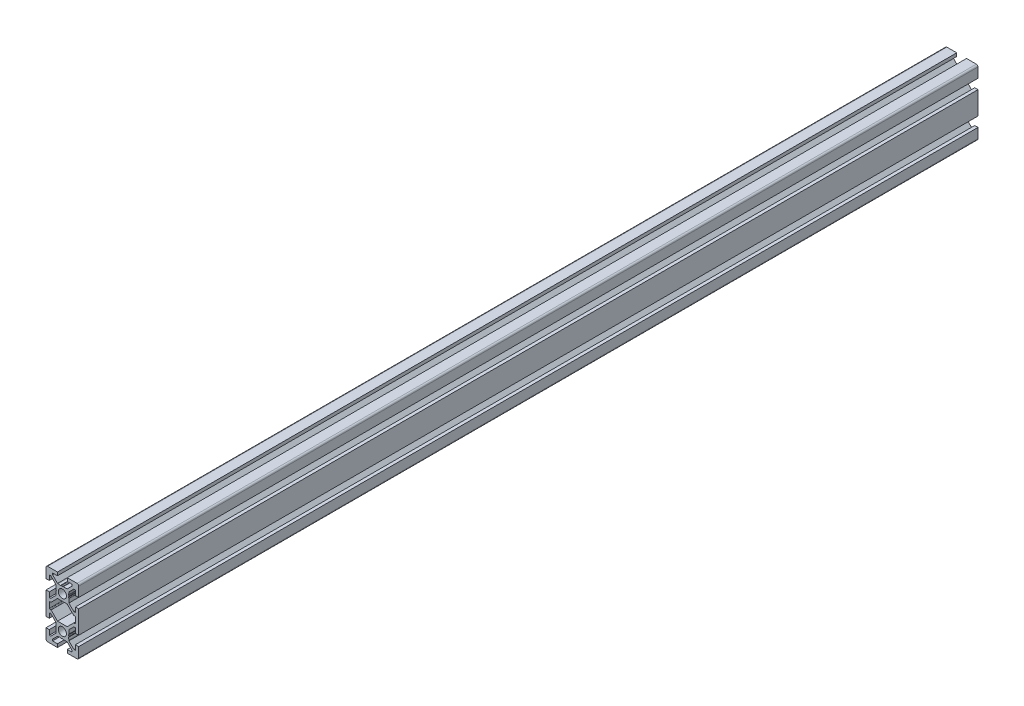
SolidWorks part; units mm, degrees
ref_plane "Front Plane" through (0, 0, 0) normal (0, 0, 1) x (1, 0, 0)
ref_plane "Top Plane" through (0, 0, 0) normal (0, 1, 0) x (1, 0, 0)
ref_plane "Right Plane" through (0, 0, 0) normal (1, 0, 0) x (0, 0, -1)
ref_plane "Plane1" through (0, 0, -600) normal (0, 0, -1) x (-1, 0, 0)
sketch "Sketch1" plane through (0, 0, -600) normal (0, 0, -1) x (-1, 0, 0)
  line L0 (8, 1.7) -> (8, -1.7)
  line L1 (7.7, -2) -> (7.0636, -2)
  line L2 (6.8515, -2.0879) -> (2.9393, -6)
  line L3 (2.9393, -6) -> (-2.9393, -6)
  line L4 (-2.9393, -6) -> (-6.8515, -2.0879)
  line L5 (-7.0636, -2) -> (-7.7, -2)
  line L6 (-8, -1.7) -> (-8, 1.7)
  line L7 (-7.7, 2) -> (-7.0636, 2)
  line L8 (-6.8515, 2.0879) -> (-2.9393, 6)
  line L9 (-2.9393, 6) -> (2.9393, 6)
  line L10 (2.9393, 6) -> (6.8515, 2.0879)
  line L11 (7.0636, 2) -> (7.7, 2)
  line L12 (10, -7) -> (10, 7)
  line L13 (10, 7) -> (8, 7)
  line L14 (8, 7) -> (8, 4)
  line L15 (8, 4) -> (7.0607, 4)
  line L16 (7.0607, 4) -> (4, 7.0607)
  line L17 (4, 7.0607) -> (4, 7.5)
  line L18 (4, 7.5) -> (3.751, 8.7811)
  line L19 (3.751, 8.7811) -> (3.933, 9.0964)
  line L20 (3.933, 9.5964) -> (3.7, 10)
  line L21 (3.7, 10) -> (3.933, 10.4036)
  line L22 (4, 10.6536) -> (4, 12.9393)
  line L23 (4, 12.9393) -> (7.0607, 16)
  line L24 (7.0607, 16) -> (8, 16)
  line L25 (8, 16) -> (8, 13)
  line L26 (8, 13) -> (10, 13)
  line L27 (10, 13) -> (10, 19)
  line L28 (9, 20) -> (3, 20)
  line L29 (3, 20) -> (3, 18)
  line L30 (3, 18) -> (6, 18)
  line L31 (6, 18) -> (6, 17.0607)
  line L32 (6, 17.0607) -> (2.9393, 14)
  line L33 (2.9393, 14) -> (2.5, 14)
  line L34 (2.5, 14) -> (1.2189, 13.751)
  line L35 (1.2189, 13.751) -> (0.9036, 13.933)
  line L36 (0.4036, 13.933) -> (0, 13.7)
  line L37 (0, 13.7) -> (-0.4036, 13.933)
  line L38 (-0.6536, 14) -> (-2.9393, 14)
  line L39 (-2.9393, 14) -> (-6, 17.0607)
  line L40 (-6, 17.0607) -> (-6, 18)
  line L41 (-6, 18) -> (-3, 18)
  line L42 (-3, 18) -> (-3, 20)
  line L43 (-3, 20) -> (-9, 20)
  line L44 (-10, 19) -> (-10, 13)
  line L45 (-10, 13) -> (-8, 13)
  line L46 (-8, 13) -> (-8, 16)
  line L47 (-8, 16) -> (-7.0607, 16)
  line L48 (-7.0607, 16) -> (-4, 12.9393)
  line L49 (-4, 12.9393) -> (-4, 12.5)
  line L50 (-4, 12.5) -> (-3.751, 11.2189)
  line L51 (-3.751, 11.2189) -> (-3.933, 10.9036)
  line L52 (-3.933, 10.4036) -> (-3.7, 10)
  line L53 (-3.7, 10) -> (-3.933, 9.5964)
  line L54 (-4, 9.3464) -> (-4, 7.0607)
  line L55 (-4, 7.0607) -> (-7.0607, 4)
  line L56 (-7.0607, 4) -> (-8, 4)
  line L57 (-8, 4) -> (-8, 7)
  line L58 (-8, 7) -> (-10, 7)
  line L59 (-10, 7) -> (-10, -7)
  line L60 (-10, -7) -> (-8, -7)
  line L61 (-8, -7) -> (-8, -4)
  line L62 (-8, -4) -> (-7.0607, -4)
  line L63 (-7.0607, -4) -> (-4, -7.0607)
  line L64 (-4, -7.0607) -> (-4, -9.3464)
  line L65 (-3.933, -9.5964) -> (-3.7, -10)
  line L66 (-3.7, -10) -> (-3.933, -10.4036)
  line L67 (-3.933, -10.9036) -> (-3.751, -11.2189)
  line L68 (-3.751, -11.2189) -> (-4, -12.5)
  line L69 (-4, -12.5) -> (-4, -12.9393)
  line L70 (-4, -12.9393) -> (-7.0607, -16)
  line L71 (-7.0607, -16) -> (-8, -16)
  line L72 (-8, -16) -> (-8, -13)
  line L73 (-8, -13) -> (-10, -13)
  line L74 (-10, -13) -> (-10, -19)
  line L75 (-9, -20) -> (-3, -20)
  line L76 (-3, -20) -> (-3, -18)
  line L77 (-3, -18) -> (-6, -18)
  line L78 (-6, -18) -> (-6, -17.0607)
  line L79 (-6, -17.0607) -> (-2.9393, -14)
  line L80 (-2.9393, -14) -> (-0.6536, -14)
  line L81 (-0.4036, -13.933) -> (0, -13.7)
  line L82 (0, -13.7) -> (0.4036, -13.933)
  line L83 (0.9036, -13.933) -> (1.2189, -13.751)
  line L84 (1.2189, -13.751) -> (2.5, -14)
  line L85 (2.5, -14) -> (2.9393, -14)
  line L86 (2.9393, -14) -> (6, -17.0607)
  line L87 (6, -17.0607) -> (6, -18)
  line L88 (6, -18) -> (3, -18)
  line L89 (3, -18) -> (3, -20)
  line L90 (3, -20) -> (9, -20)
  line L91 (10, -19) -> (10, -13)
  line L92 (10, -13) -> (8, -13)
  line L93 (8, -13) -> (8, -16)
  line L94 (8, -16) -> (7.0607, -16)
  line L95 (7.0607, -16) -> (4, -12.9393)
  line L96 (4, -12.9393) -> (4, -10.6536)
  line L97 (3.933, -10.4036) -> (3.7, -10)
  line L98 (3.7, -10) -> (3.933, -9.5964)
  line L99 (3.933, -9.0964) -> (3.751, -8.7811)
  line L100 (3.751, -8.7811) -> (4, -7.5)
  line L101 (4, -7.5) -> (4, -7.0607)
  line L102 (4, -7.0607) -> (7.0607, -4)
  line L103 (7.0607, -4) -> (8, -4)
  line L104 (8, -4) -> (8, -7)
  line L105 (8, -7) -> (10, -7)
  circle A0 centre (0, -10) radius 2.5
  circle A1 centre (0, 10) radius 2.5
  arc A2 (7.7, 2) -> (8, 1.7) centre (7.7, 1.7) cw
  arc A3 (8, -1.7) -> (7.7, -2) centre (7.7, -1.7) cw
  arc A4 (7.0636, -2) -> (6.8515, -2.0879) centre (7.0636, -2.3) ccw
  arc A5 (-6.8515, -2.0879) -> (-7.0636, -2) centre (-7.0636, -2.3) ccw
  arc A6 (-7.7, -2) -> (-8, -1.7) centre (-7.7, -1.7) cw
  arc A7 (-8, 1.7) -> (-7.7, 2) centre (-7.7, 1.7) cw
  arc A8 (-7.0636, 2) -> (-6.8515, 2.0879) centre (-7.0636, 2.3) ccw
  arc A9 (6.8515, 2.0879) -> (7.0636, 2) centre (7.0636, 2.3) ccw
  arc A10 (3.933, 9.0964) -> (3.933, 9.5964) centre (3.5, 9.3464) ccw
  arc A11 (3.933, 10.4036) -> (4, 10.6536) centre (3.5, 10.6536) ccw
  arc A12 (10, 19) -> (9, 20) centre (9, 19) ccw
  arc A13 (0.9036, 13.933) -> (0.4036, 13.933) centre (0.6536, 13.5) ccw
  arc A14 (-0.4036, 13.933) -> (-0.6536, 14) centre (-0.6536, 13.5) ccw
  arc A15 (-9, 20) -> (-10, 19) centre (-9, 19) ccw
  arc A16 (-3.933, 10.9036) -> (-3.933, 10.4036) centre (-3.5, 10.6536) ccw
  arc A17 (-3.933, 9.5964) -> (-4, 9.3464) centre (-3.5, 9.3464) ccw
  arc A18 (-4, -9.3464) -> (-3.933, -9.5964) centre (-3.5, -9.3464) ccw
  arc A19 (-3.933, -10.4036) -> (-3.933, -10.9036) centre (-3.5, -10.6536) ccw
  arc A20 (-10, -19) -> (-9, -20) centre (-9, -19) ccw
  arc A21 (-0.6536, -14) -> (-0.4036, -13.933) centre (-0.6536, -13.5) ccw
  arc A22 (0.4036, -13.933) -> (0.9036, -13.933) centre (0.6536, -13.5) ccw
  arc A23 (9, -20) -> (10, -19) centre (9, -19) ccw
  arc A24 (4, -10.6536) -> (3.933, -10.4036) centre (3.5, -10.6536) ccw
  arc A25 (3.933, -9.5964) -> (3.933, -9.0964) centre (3.5, -9.3464) ccw
  dimension "D1" = 5
  dimension "D3" = 0.3
  dimension "D4" = 0.3
  dimension "D5" = 0.3
  dimension "D6" = 0.3
  dimension "D7" = 0.3
  dimension "D8" = 0.3
  dimension "D9" = 0.3
  dimension "D10" = 0.5
  dimension "D11" = 0.5
  dimension "D12" = 1
  dimension "D13" = 0.5
  dimension "D14" = 0.5
  dimension "D15" = 1
  dimension "D16" = 0.5
  dimension "D17" = 0.5
  dimension "D18" = 0.5
  dimension "D19" = 0.5
  dimension "D20" = 0.4036
  dimension "D21" = 0.5
  dimension "D22" = 0.5
  dimension "D23" = 1
  dimension "D24" = 0.5
  dimension "D25" = 0.5
  dimension "D26" = 0.4036
  dimension "D27" = 0.6536
  dimension "D28" = 0.6536
  dimension "D29" = 0.9036
  dimension "D30" = 0.9036
  dimension "D31" = 1.2189
  dimension "D32" = 1.2189
  dimension "D33" = 2.5
  dimension "D34" = 2.5
  dimension "D35" = 2.9393
  dimension "D36" = 2.9393
  dimension "D37" = 3
  dimension "D38" = 3.5
  dimension "D39" = 6
  dimension "D40" = 6.8515
  dimension "D41" = 3.7
  dimension "D42" = 3.7
  dimension "D43" = 3.751
  dimension "D44" = 3.751
  dimension "D45" = 3.933
  dimension "D46" = 3.933
  dimension "D47" = 6.8515
  dimension "D48" = 7.0607
  dimension "D49" = 7.0607
  dimension "D50" = 7.0636
  dimension "D51" = 7.0636
  dimension "D52" = 8
  dimension "D53" = 10
  dimension "D54" = 3
  dimension "D55" = 4
  dimension "D56" = 6
  dimension "D57" = 6.8515
  dimension "D58" = 6.8515
  dimension "D59" = 7.0607
  dimension "D60" = 7.0607
  dimension "D61" = 0.4036
  dimension "D62" = 0.4036
  dimension "D63" = 0.6536
  dimension "D64" = 0.6536
  dimension "D65" = 2.9393
  dimension "D66" = 2.9393
  dimension "D67" = 8
  dimension "D68" = 2
  dimension "D69" = 3.5
  dimension "D70" = 3.5
  dimension "D71" = 3.7
  dimension "D72" = 3.7
  dimension "D73" = 3.751
  dimension "D74" = 3.751
  dimension "D75" = 3.933
  dimension "D76" = 3.933
  dimension "D77" = 4
  dimension "D78" = 6
  dimension "D79" = 7
  dimension "D80" = 7.0607
  dimension "D81" = 7.0607
  dimension "D82" = 7.5
  dimension "D83" = 8.7811
  dimension "D84" = 9.0964
  dimension "D85" = 9.3464
  dimension "D86" = 9.3464
  dimension "D87" = 9.5964
  dimension "D88" = 9.5964
  dimension "D89" = 10.4036
  dimension "D90" = 12.5
  dimension "D91" = 13
  dimension "D92" = 13.5
  dimension "D93" = 13.5
  dimension "D94" = 18
  dimension "D95" = 20
  dimension "D96" = 2
  dimension "D97" = 4
  dimension "D98" = 6
  dimension "D99" = 7
  dimension "D100" = 7.0607
  dimension "D101" = 7.0607
  dimension "D102" = 7.5
  dimension "D103" = 8.7811
  dimension "D104" = 9.0964
  dimension "D105" = 9.3464
  dimension "D106" = 9.3464
  dimension "D107" = 9.5964
  dimension "D108" = 9.5964
  dimension "D109" = 10.4036
  dimension "D110" = 12.5
  dimension "D111" = 13
  dimension "D112" = 18
extrude "Boss-Extrude1" add sketch "Sketch1" against normal blind 550
